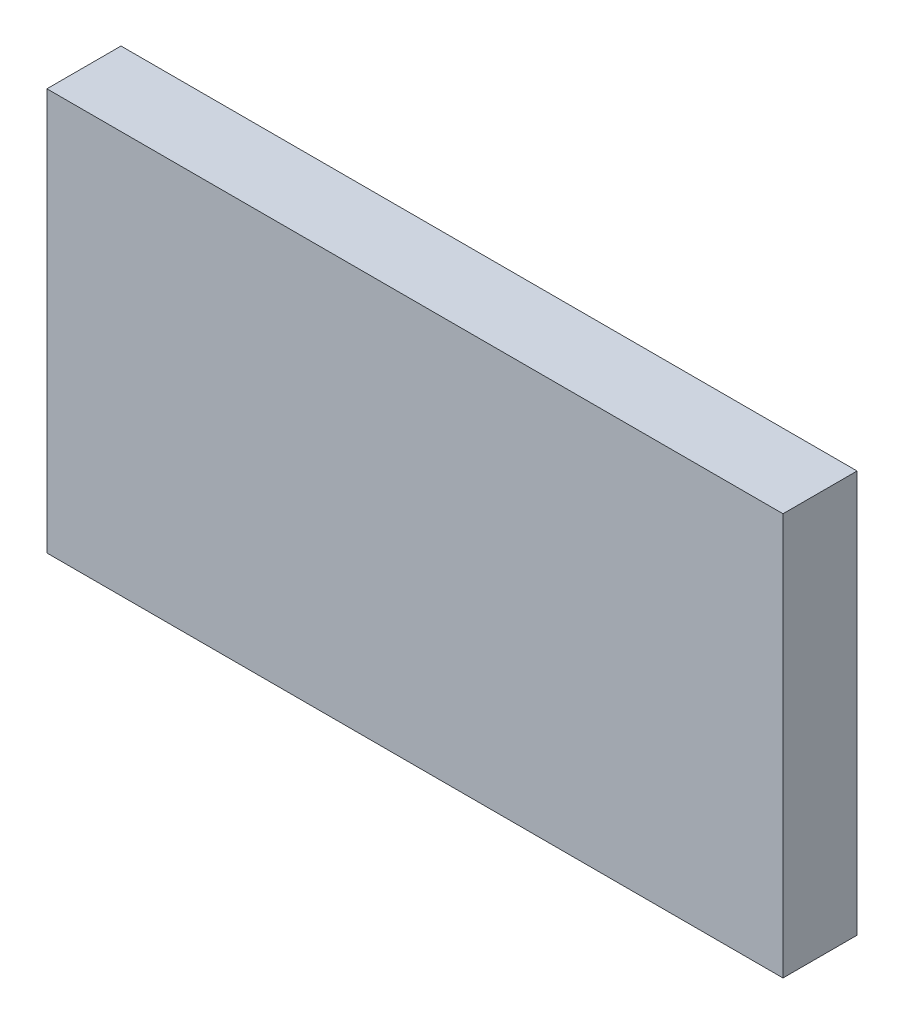
SolidWorks part; units mm, degrees
other "Target"
other "Stock"
ref_plane "Front Plane" through (0, 0, 0) normal (0, 0, 1) x (1, 0, 0)
ref_plane "Top Plane" through (0, 0, 0) normal (0, 1, 0) x (1, 0, 0)
ref_plane "Right Plane" through (0, 0, 0) normal (1, 0, 0) x (0, 0, -1)
sketch "Sketch1" plane through (0, 0, 0) normal (0, 0, 1) x (1, 0, 0)
  line L1 (-75, 40) -> (75, 40)
  line L2 (-75, 40) -> (-75, -40)
  line L3 (-75, -40) -> (75, -40)
  line L4 (75, 40) -> (75, -40)
  line L5 (-75, 40) -> (75, -40) construction
  line L6 (-75, -40) -> (75, 40) construction
  point P0 (0, 0)
  dimension "D1" = 150
  dimension "D2" = 80
extrude "Boss-Extrude1" add sketch "Sketch1" along normal blind 10
fillet "Fillet1" radius 3 4 edges at (75, -40, 5) (75, 40, 5) (-75, 40, 5) (-75, -40, 5)
hole_wizard "Ø5.0 (5) Diameter Hole1" positions "Sketch3" profile "Sketch2" hole size "Ø5.0" standard "ANSI Metric" end condition through all
sketch "Sketch3" plane through (0, 0, 10) normal (0, 0, 1) x (1, 0, 0)
  line L0 (-72, -40) -> (72, -40) construction
  line L1 (-75, 37) -> (-75, -37) construction
  line L2 (72, 40) -> (-72, 40) construction
  line L3 (75, -37) -> (75, 37) construction
  point P0 (-70, -35)
  point P2 (-70, 35)
  point P4 (70, 35)
  point P6 (70, -35)
  dimension "D1" = 5
  dimension "D2" = 5
  dimension "D3" = 5
  dimension "D4" = 5
  dimension "D5" = 5
  dimension "D6" = 5
  dimension "D7" = 5
  dimension "D8" = 5
sketch "Sketch2" plane through (-70, -35, 10) normal (1, 0, 0) x (0, -1, 0)
  line L0 (0, 0) -> (0, 10)
  line L1 (0, 10) -> (2.5, 10)
  line L2 (2.5, 10) -> (2.5, 0)
  line L5 (2.5, 0) -> (0, 0)
  line L11 (0, -6.35) -> (0, 107.95) construction
  dimension "Thru Hole Dia." = 5
  dimension "Thru Hole Depth" = 10
sketch "Sketch5" plane through (0, 0, 10) normal (0, 0, 1) x (1, 0, 0)
  line L0 (72, 40) -> (-72, 40) construction
  line L1 (-59.0455, 34) -> (59.0455, 34)
  line L2 (-69, 24.0455) -> (-69, -24.0455)
  line L3 (-59.0455, -34) -> (59.0455, -34)
  line L4 (69, 24.0455) -> (69, -24.0455)
  line L5 (-69, 34) -> (69, -34) construction
  line L6 (-69, -34) -> (69, 34) construction
  line L7 (75, -37) -> (75, 37) construction
  arc A0 (-59.0455, 34) -> (-69, 24.0455) centre (-70, 35) cw
  arc A1 (-59.0455, -34) -> (-69, -24.0455) centre (-70, -35) ccw
  arc A2 (69, -24.0455) -> (59.0455, -34) centre (70, -35) ccw
  arc A3 (59.0455, 34) -> (69, 24.0455) centre (70, 35) ccw
  point P0 (0, 0)
  point P6 (0, 40)
  point P11 (-70, 35)
  point P12 (-70, -35)
  point P14 (70, -35)
  point P16 (70, 35)
  dimension "D3" = 11
  dimension "D1" = 6
  dimension "D2" = 6
  dimension "D4" = 138
  dimension "D5" = 68
extrude "Cut-Extrude1" cut sketch "Sketch5" against normal blind 8
fillet "Fillet2" radius 3.5 8 edges at (-69, -24.0455, 6) (-59.0455, -34, 6) (59.0455, -34, 6) (69, -24.0455, 6) (69, 24.0455, 6) (59.0455, 34, 6) (-59.0455, 34, 6) (-69, 24.0455, 6)
sketch "Sketch8" plane through (0, 0, 10) normal (0, 0, 1) x (1, 0, 0)
  line L1 (-76.962, 42.037) -> (76.962, 42.037)
  line L2 (-76.962, 42.037) -> (-76.962, -42.037)
  line L3 (-76.962, -42.037) -> (76.962, -42.037)
  line L4 (76.962, 42.037) -> (76.962, -42.037)
  line L5 (-76.962, 42.037) -> (76.962, -42.037) construction
  line L6 (-76.962, -42.037) -> (76.962, 42.037) construction
  point P0 (0, 0)
extrude "Boss-Extrude3" add sketch "Sketch8" along normal blind 0.508 and the other way blind 14.986 separate body
